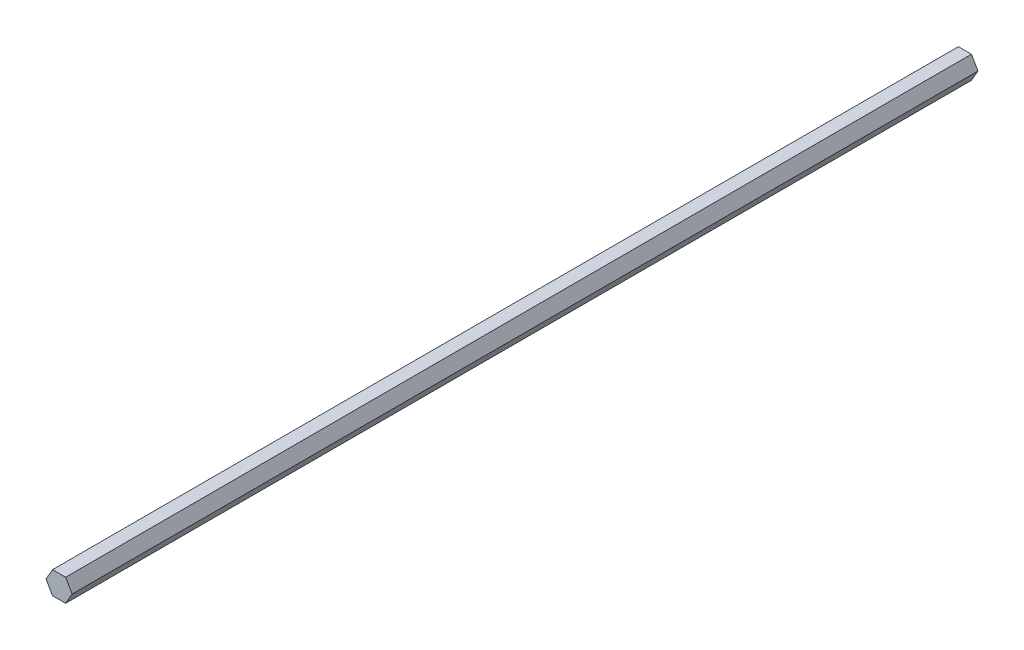
SolidWorks part; units mm, degrees
ref_plane "Front Plane" through (0, 0, 0) normal (0, 0, 1) x (1, 0, 0)
ref_plane "Top Plane" through (0, 0, 0) normal (0, 1, 0) x (1, 0, 0)
ref_plane "Right Plane" through (0, 0, 0) normal (1, 0, 0) x (0, 0, -1)
sketch "Sketch1" plane through (0, 0, 0) normal (0, 0, 1) x (1, 0, 0)
  line L1 (7.3323, 0) -> (3.6662, 6.35)
  line L2 (3.6662, 6.35) -> (-3.6662, 6.35)
  line L3 (-3.6662, 6.35) -> (-7.3323, 0)
  line L4 (-7.3323, 0) -> (-3.6662, -6.35)
  line L5 (-3.6662, -6.35) -> (3.6662, -6.35)
  line L6 (3.6662, -6.35) -> (7.3323, 0)
  circle A0 centre (0, 0) radius 6.35 construction
  dimension "D1" = 12.7
extrude "Boss-Extrude1" add sketch "Sketch1" along normal blind 508
sketch "Sketch3" plane through (0, 0, 508) normal (0, 0, 1) x (1, 0, 0)
  line L0 (-5.4993, 3.175) -> (5.4993, -3.175)
  line L1 (-3.6662, 6.35) -> (-7.3323, 0) construction
  line L2 (3.6662, -6.35) -> (7.3323, 0) construction
  line L3 (-5.4993, -3.175) -> (5.4993, 3.175)
  line L4 (-7.3323, 0) -> (-3.6662, -6.35) construction
  line L5 (7.3323, 0) -> (3.6662, 6.35) construction
  line L6 (0, 6.35) -> (0, -6.35)
  line L7 (3.6662, 6.35) -> (-3.6662, 6.35) construction
  line L8 (-3.6662, -6.35) -> (3.6662, -6.35) construction
  line L9 (-7.3323, 0) -> (7.3323, 0)
  line L10 (-3.6662, 6.35) -> (3.6662, -6.35)
  line L11 (-3.6662, -6.35) -> (3.6662, 6.35)
